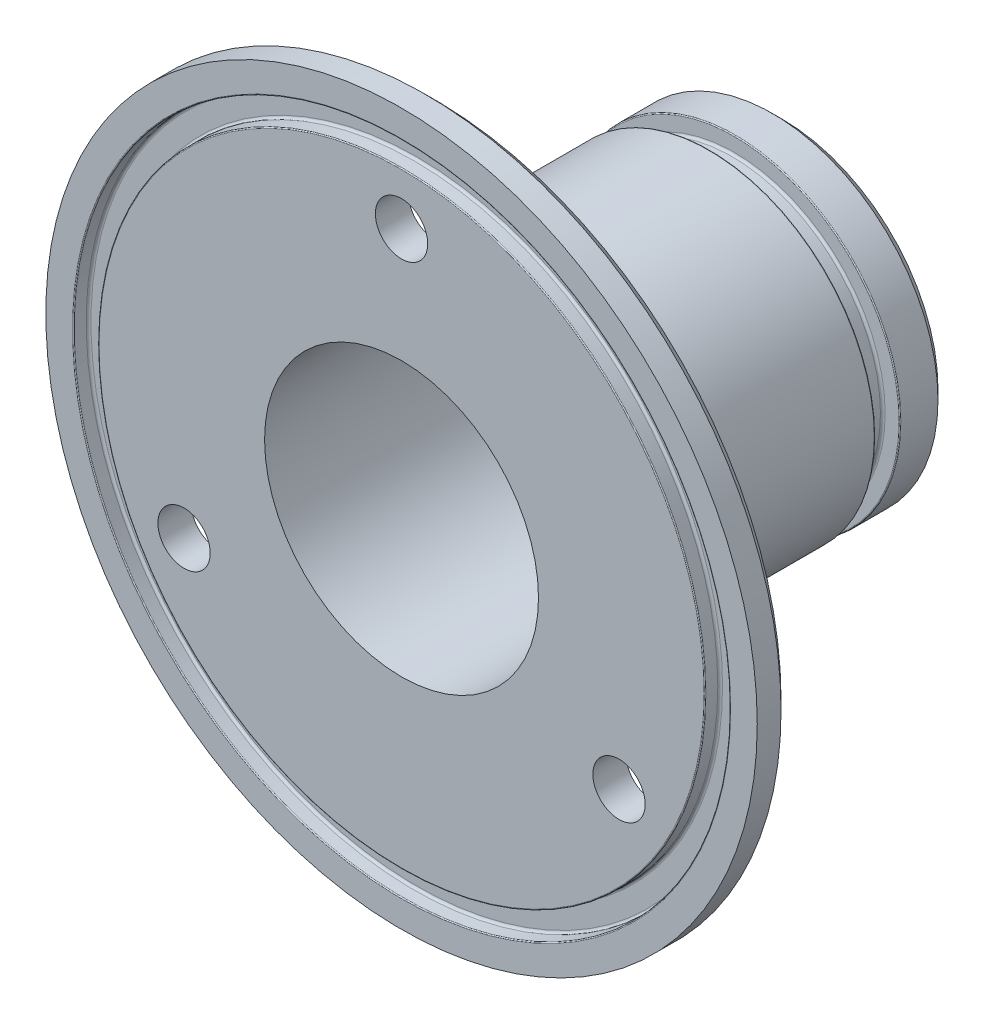
SolidWorks part; units mm, degrees
ref_plane "Front Plane" through (0, 0, 0) normal (0, 0, 1) x (1, 0, 0)
ref_plane "Top Plane" through (0, 0, 0) normal (0, 1, 0) x (1, 0, 0)
ref_plane "Right Plane" through (0, 0, 0) normal (1, 0, 0) x (0, 0, -1)
sketch "Sketch1" plane through (0, 0, 0) normal (0, 0, 1) x (1, 0, 0)
  circle A0 centre (0, 0) radius 17.4
  circle A1 centre (0, 0) radius 14.4
  dimension "D1" = 34.8
  dimension "3" = 3
extrude "Boss-Extrude1" add sketch "Sketch1" along normal blind 40
sketch "Sketch2" plane through (0, 0, 40) normal (0, 0, 1) x (1, 0, 0)
  circle A0 centre (0, 0) radius 37.4
  circle A1 centre (0, 0) radius 17.4 construction
  circle A2 centre (0, 0) radius 17.4
  dimension "D1" = 20
extrude "Boss-Extrude2" add sketch "Sketch2" against normal blind 3.5 separate body
hole_wizard "M5 Clearance Hole1" positions "Sketch3" profile "Sketch4" hole size "M5" standard "ISO" end condition through all
sketch "Sketch3" plane through (0, 0, 36.5) normal (0, 0, -1) x (-1, 0, 0)
  line L0 (0, 17.4) -> (0, 37.4) construction
  line L1 (0, 26.4) -> (0, 0) construction
  circle A0 centre (0, 0) radius 17.4 construction
  circle A1 centre (0, 0) radius 37.4 construction
  circle A2 centre (0, 0) radius 26.4 construction
  point P0 (0, 26.4)
  dimension "D1" = 52.8
sketch "Sketch4" plane through (0, 26.4, 36.5) normal (1, 0, 0) x (0, 1, 0)
  line L0 (0, 0) -> (0, 3.5)
  line L1 (0, 3.5) -> (2.75, 3.5)
  line L2 (2.75, 3.5) -> (2.75, 0)
  line L5 (2.75, 0) -> (0, 0)
  line L11 (0, -6.35) -> (0, 107.95) construction
  dimension "Thru Hole Dia." = 5.5
  dimension "Thru Hole Depth" = 3.5
pattern_circular "CirPattern1" count 3 over 360 about axis through (0, 0, 0) along (0, 0, 1) of "M5 Clearance Hole1"
sketch "Sketch5" plane through (0, 0, 0) normal (0, 1, 0) x (1, 0, 0)
  line L0 (-17.4, 0) -> (-17.4, -36.5) construction
  line L1 (37.4, -36.5) -> (-37.4, -36.5) construction
  line L2 (-17.4, 0) -> (-17.4, -40) construction
  line L3 (-17.4, -5) -> (-15.6, -5)
  line L4 (-15.6, -5) -> (-15.6, -7.6)
  line L5 (-15.6, -7.6) -> (-17.4, -7.6)
  line L6 (-17.4, -7.6) -> (-17.4, -5) construction
  line L7 (-17.4, -5) -> (-17.4, -7.6)
  dimension "D1" = 1.8
  dimension "D2" = 2.6
  dimension "D3" = 5
revolve "Cut-Revolve1" cut sketch "Sketch5" angle 360 about axis through (0, 0, 40) along (0, 0, -1)
fillet "Fillet1" radius 0.1 2 edges at (17.4, 0, 5) (17.4, 0, 7.6)
fillet "Fillet2" radius 0.25 2 edges at (15.6, 0, 5) (15.6, 0, 7.6)
combine bodies "Combine1" operation type add bodies to combine 105 104
sketch "Sketch6" plane through (0, 0, 40) normal (0, 0, 1) x (1, 0, 0)
  circle A0 centre (0, 0) radius 31.9
  circle A1 centre (0, 0) radius 34.5
  dimension "D1" = 69
  dimension "D2" = 2.6
extrude "Cut-Extrude1" cut sketch "Sketch6" against normal blind 1.6
fillet "Fillet3" radius 0.25 2 edges at (31.9, 0, 38.4) (34.5, 0, 38.4)
fillet "Fillet4" radius 0.1 2 edges at (31.9, 0, 40) (34.5, 0, 40)
chamfer "Chamfer1" distance 1 angle 45 1 edges at (37.4, 0, 36.5)
fillet "Fillet5" radius 1 1 edges at (17.4, 0, 36.5)
chamfer "Chamfer2" distance 1 angle 45 1 edges at (17.4, 0, 0)
